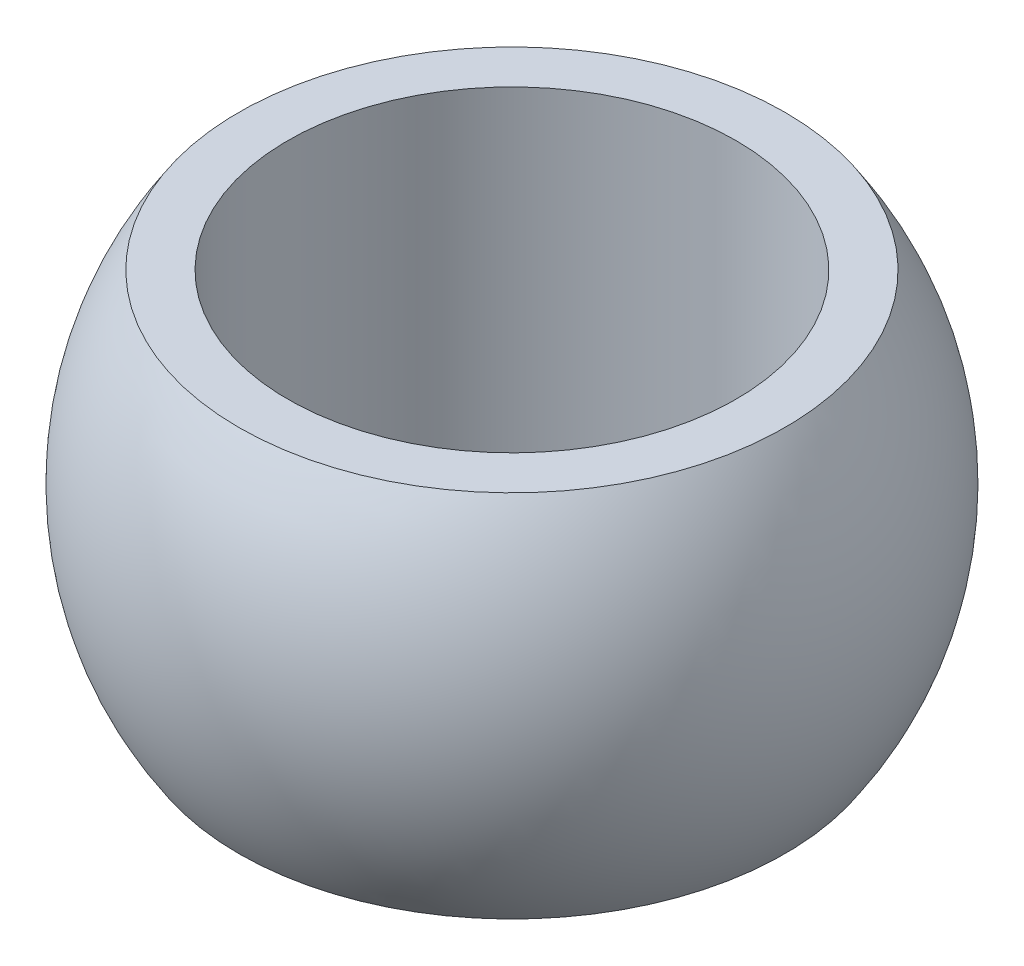
SolidWorks part; units mm, degrees
ref_plane "Face" through (0, 0, 0) normal (0, 0, 1) x (1, 0, 0)
ref_plane "Dessus" through (0, 0, 0) normal (0, 1, 0) x (1, 0, 0)
ref_plane "Droite" through (0, 0, 0) normal (1, 0, 0) x (0, 0, -1)
sketch "Esquisse1" plane through (0, 0, 0) normal (0, 0, 1) x (1, 0, 0)
  line L0 (0, -15.3398) -> (0, 15.7895) construction
  line L1 (8.5, -7) -> (10.3562, -7)
  line L2 (8.5, 7) -> (10.3562, 7)
  line L3 (0, 0) -> (17.9597, 0) construction
  line L5 (8.5, 7) -> (8.5, -7)
  arc A0 (10.3562, -7) -> (10.3562, 7) centre (0, 0) ccw
  point P8 (8.5, 0)
  dimension "D1" = 25
  dimension "D2" = 8.5
  dimension "D3" = 7
revolve "Révolution1" add sketch "Esquisse1" angle 360 about L0
